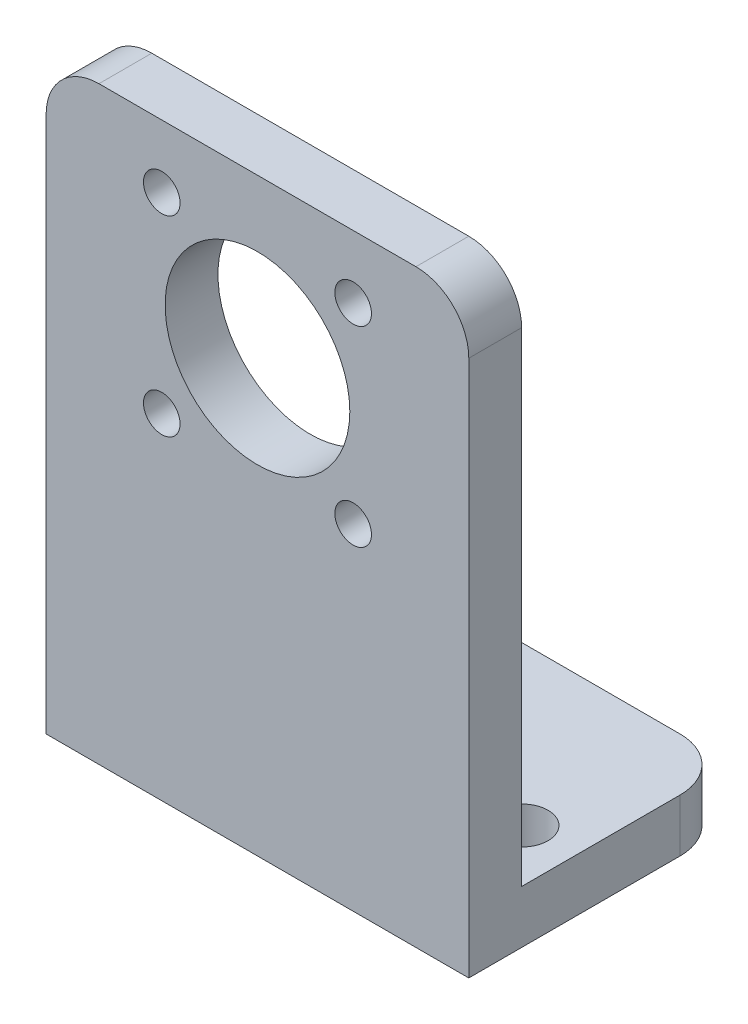
SolidWorks part; units mm, degrees
material "6061-T6 (SS)"
ref_plane "Front Plane" through (0, 0, 0) normal (0, 0, 1) x (1, 0, 0)
ref_plane "Top Plane" through (0, 0, 0) normal (0, 1, 0) x (1, 0, 0)
ref_plane "Right Plane" through (0, 0, 0) normal (1, 0, 0) x (0, 0, -1)
sketch "Sketch1" plane through (0, 0, 0) normal (0, 0, 1) x (1, 0, 0)
  line L0 (-12.7, -25.908) -> (12.7, -25.908)
  line L1 (-12.7, 9.525) -> (12.7, 9.525)
  line L2 (0, 0) -> (0, -25.908) construction
  line L3 (-12.7, 9.525) -> (-12.7, -25.908)
  line L4 (12.7, 9.525) -> (12.7, -25.908)
  circle A0 centre (0, 0) radius 5.55
  dimension "D2" = 11.1
  dimension "D3" = 9.525
  dimension "D1" = 25.908
  dimension "D5" = 25.4
extrude "Boss-Extrude1" add sketch "Sketch1" along normal blind 3.175
sketch "Sketch3" plane through (0, 0, 0) normal (0, 0, -1) x (-1, 0, 0)
  line L0 (-12.7, -25.908) -> (-12.7, 9.525) construction
  line L1 (12.7, -25.908) -> (-12.7, -25.908)
  line L2 (12.7, -25.908) -> (12.7, -22.733)
  line L3 (12.7, -22.733) -> (-12.7, -22.733)
  line L4 (-12.7, -25.908) -> (-12.7, -22.733)
  dimension "D1" = 3.175
extrude "Boss-Extrude2" add sketch "Sketch3" along normal blind 12.7
fillet "Fillet1" radius 3.175 4 edges at (-12.7, 9.525, 1.5875) (12.7, 9.525, 1.5875) (12.7, -24.3205, -12.7) (-12.7, -24.3205, -12.7)
hole_wizard "M2 Clearance Hole1" positions "Sketch7" profile "Sketch8" hole size "M2" standard "ANSI Metric" end condition through all
sketch "Sketch7" plane through (0, -25.908, 3.175) normal (0, 0, 1) x (1, 0, 0)
  point P0 (5.75, 31.658)
  point P2 (-5.75, 31.658)
  point P4 (5.75, 20.158)
  point P6 (-5.75, 20.158)
sketch "Sketch8" plane through (5.75, 5.75, 3.175) normal (1, 0, 0) x (0, -1, 0)
  line L0 (0, 0) -> (0, 15.875)
  line L1 (0, 15.875) -> (1.1, 15.875)
  line L2 (1.1, 15.875) -> (1.1, 0)
  line L3 (1.1, 0) -> (0, 0)
  line L4 (0, -6.35) -> (0, 107.95) construction
  dimension "Thru Hole Dia." = 2.2
  dimension "Thru Hole Depth" = 15.875
hole_wizard "#4 Clearance Hole1" positions "Sketch11" profile "Sketch12" hole size "#4" standard "ANSI Inch" end condition through all
sketch "Sketch11" plane through (0, -22.733, 0) normal (0, 1, 0) x (1, 0, 0)
  line L4 (-12.7, -3.175) -> (12.7, -3.175) construction
  line L5 (-12.7, 0) -> (12.7, 0) construction
  point P2 (0, 9.525)
  point P23 (0, 0)
  dimension "D1" = 12.7
sketch "Sketch12" plane through (0, -22.733, -9.525) normal (1, 0, 0) x (0, 0, 1)
  line L0 (0, 0) -> (0, 3.175)
  line L1 (0, 3.175) -> (1.4732, 3.175)
  line L2 (1.4732, 3.175) -> (1.4732, 0)
  line L5 (1.4732, 0) -> (0, 0)
  line L11 (0, -6.35) -> (0, 107.95) construction
  dimension "Thru Hole Dia." = 2.9464
  dimension "Thru Hole Depth" = 3.175
hole_wizard "1/8 (0.1250) Dowel Hole1" positions "Sketch13" profile "Sketch14" hole size "1/8" standard "ANSI Inch"
sketch "Sketch13" plane through (0, -22.733, 0) normal (0, 1, 0) x (1, 0, 0)
  line L0 (-9.525, 3.175) -> (0, 0)
  line L1 (0, 0) -> (9.525, 3.175)
  line L3 (9.525, -3.175) -> (-9.525, -3.175) construction
  point P0 (9.525, 3.175)
  point P2 (-9.525, 3.175)
  dimension "D1" = 6.35
  dimension "D2" = 19.05
sketch "Sketch14" plane through (9.525, -22.733, -3.175) normal (1, 0, 0) x (0, 0, 1)
  line L0 (0, 0) -> (0, 5.0179)
  line L1 (0, 5.0179) -> (1.5875, 4.064)
  line L2 (1.5875, 4.064) -> (1.5875, 0)
  line L5 (1.5875, 0) -> (0, 0)
  line L10 (0, 5.0179) -> (-1.5875, 4.064) construction
  line L11 (0, -6.35) -> (0, 107.95) construction
  dimension "Hole Dia." = 3.175
  dimension "Hole Depth" = 4.064
  dimension "Drill Angle" = 118
